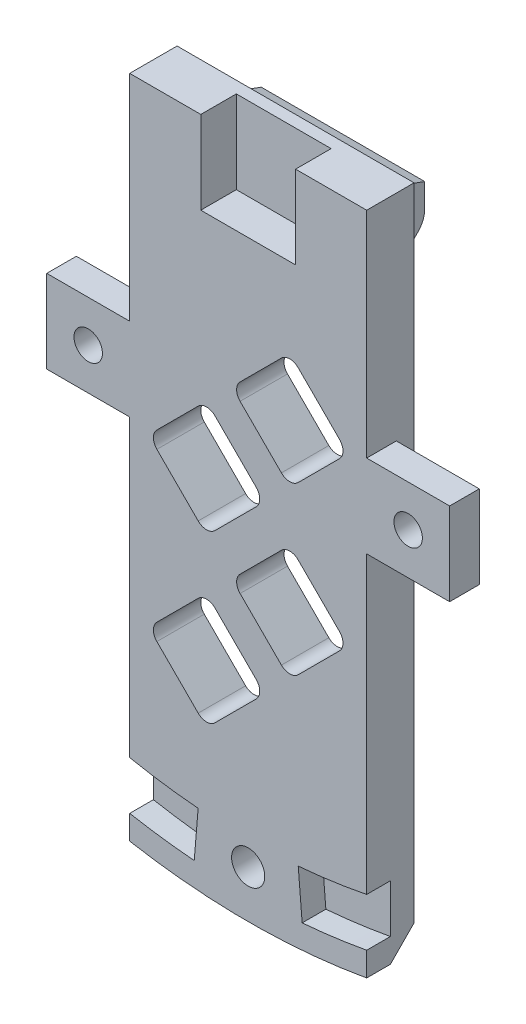
SolidWorks part; units mm, degrees
ref_plane "Front Plane" through (0, 0, 0) normal (0, 0, 1) x (1, 0, 0)
ref_plane "Top Plane" through (0, 0, 0) normal (0, 1, 0) x (1, 0, 0)
ref_plane "Right Plane" through (0, 0, 0) normal (1, 0, 0) x (0, 0, -1)
sketch "Sketch1" plane through (0, 0, 0) normal (0, 0, 1) x (1, 0, 0)
  line L0 (-12.7, -71.2673) -> (-12.7, 71.2673)
  line L1 (12.7, 71.2673) -> (12.7, -71.2673)
  line L2 (-12.7, 0) -> (12.7, 0)
  line L3 (0, 0) -> (0, 40.2261) construction
  arc A0 (-12.7, -71.2673) -> (12.7, -71.2673) centre (0, 0) ccw
  arc A1 (12.7, 71.2673) -> (-12.7, 71.2673) centre (0, 0) ccw
  circle A2 centre (0, 11.43) radius 7.62 construction
  dimension "D1" = 144.78
  dimension "D4" = 15.24
  dimension "D2" = 25.4
  dimension "D3" = 11.43
extrude "Boss-Extrude1" add sketch "Sketch1" along normal blind 5.08 contours L0 A0 L1 L2
sketch "Sketch4" plane through (0, 0, 0) normal (1, 0, 0) x (0, 0, -1)
  line L0 (0, -2.54) -> (5.08, -4.389)
  line L1 (5.08, -4.389) -> (5.08, -6.929)
  line L2 (4.3361, -8.725) -> (0.7439, -12.3171)
  line L3 (0, -14.1132) -> (0, -2.54)
  line L4 (0, -71.2673) -> (0, 0)
  line L5 (0, 0) -> (-5.08, 0)
  line L6 (-5.08, 0) -> (-5.08, -71.2673)
  line L7 (-5.08, -71.2673) -> (0, -71.2673)
  line L8 (0, -71.2673) -> (0, -14.1132)
  line L9 (0, 0) -> (-5.08, 0)
  line L10 (-5.08, 0) -> (-5.08, -71.2673)
  line L11 (-5.08, -71.2673) -> (0, -71.2673)
  arc A0 (0, -14.1132) -> (0.7439, -12.3171) centre (2.54, -14.1132) cw
  arc A1 (4.3361, -8.725) -> (5.08, -6.929) centre (2.54, -6.929) ccw
  dimension "D4" = 2.54
  dimension "D2" = 70
  dimension "D3" = 45
  dimension "D5" = 2.54
  dimension "D6" = 2.54
  dimension "D7" = 5.08
  dimension "D1" = 0
extrude "Boss-Extrude2" add sketch "Sketch4" along normal mid plane 17.526 contours L2 A1 L1 L0 L3 A0
chamfer "Chamfer1" distance 2.54 angle 45 1 edges at (0, -72.39, 0)
sketch "Sketch5" plane through (0, 0, 0) normal (0, 0, -1) x (-1, 0, 0)
  line L0 (-9.788, -42.3613) -> (-5.3581, -46.7913)
  line L1 (-9.788, -40.5653) -> (-5.3581, -36.1353)
  line L2 (-3.562, -46.7913) -> (0.8679, -42.3613)
  line L3 (-3.562, -36.1353) -> (0.8679, -40.5653)
  line L4 (-0.8679, -33.4412) -> (3.562, -37.8712)
  line L5 (-0.8679, -31.6452) -> (3.562, -27.2152)
  line L6 (5.3581, -37.8712) -> (9.788, -33.4412)
  line L7 (5.3581, -27.2152) -> (9.788, -31.6452)
  line L8 (-9.788, -24.5212) -> (-5.3581, -28.9511)
  line L9 (-9.788, -22.7251) -> (-5.3581, -18.2951)
  line L10 (-3.562, -28.9511) -> (0.8679, -24.5212)
  line L11 (-3.562, -18.2951) -> (0.8679, -22.7251)
  line L12 (-0.8679, -51.2814) -> (3.562, -55.7114)
  line L13 (-0.8679, -49.4854) -> (3.562, -45.0554)
  line L14 (5.3581, -55.7114) -> (9.788, -51.2814)
  line L15 (5.3581, -45.0554) -> (9.788, -49.4854)
  line L16 (-12.7, 0) -> (-12.7, -68.6858) construction
  line L17 (12.7, -68.6858) -> (12.7, 0) construction
  line L18 (-8.763, -14.1132) -> (8.763, -14.1132) construction
  arc A0 (-3.562, -36.1353) -> (-5.3581, -36.1353) centre (-4.46, -37.0333) ccw
  arc A1 (0.8679, -40.5653) -> (0.8679, -42.3613) centre (-0.0301, -41.4633) cw
  arc A2 (-3.562, -46.7913) -> (-5.3581, -46.7913) centre (-4.46, -45.8933) cw
  arc A3 (-9.788, -40.5653) -> (-9.788, -42.3613) centre (-8.89, -41.4633) ccw
  arc A4 (9.788, -51.2814) -> (9.788, -49.4854) centre (8.89, -50.3834) ccw
  arc A5 (5.3581, -55.7114) -> (3.562, -55.7114) centre (4.46, -54.8133) cw
  arc A6 (-0.8679, -51.2814) -> (-0.8679, -49.4854) centre (0.0301, -50.3834) cw
  arc A7 (5.3581, -45.0554) -> (3.562, -45.0554) centre (4.46, -45.9534) ccw
  arc A8 (-3.562, -18.2951) -> (-5.3581, -18.2951) centre (-4.46, -19.1932) ccw
  arc A9 (-9.788, -24.5212) -> (-9.788, -22.7251) centre (-8.89, -23.6231) cw
  arc A10 (0.8679, -22.7251) -> (0.8679, -24.5212) centre (-0.0301, -23.6231) cw
  arc A11 (-3.562, -28.9511) -> (-5.3581, -28.9511) centre (-4.46, -28.0531) cw
  arc A12 (5.3581, -37.8712) -> (3.562, -37.8712) centre (4.46, -36.9732) cw
  arc A13 (9.788, -31.6452) -> (9.788, -33.4412) centre (8.89, -32.5432) cw
  arc A14 (5.3581, -27.2152) -> (3.562, -27.2152) centre (4.46, -28.1133) ccw
  arc A15 (-0.8679, -33.4412) -> (-0.8679, -31.6452) centre (0.0301, -32.5432) cw
  point P10 (-4.46, -47.6893)
  point P13 (-10.6861, -41.4633)
  dimension "D2" = 1.27
  dimension "D3" = 1.27
  dimension "D4" = 3.81
  dimension "D5" = 3.81
  dimension "D6" = 3.81
  dimension "D7" = 45
  dimension "D1" = 3.81
  dimension "D8" = 3.81
  dimension "D9" = 5.08
extrude "Cut-Extrude2" cut sketch "Sketch5" against normal blind 6.35
sketch "Sketch6" plane through (0, 0, 5.08) normal (0, 0, 1) x (1, 0, 0)
  line L0 (-12.7, 0) -> (12.7, 0) construction
  line L1 (-5.08, 0) -> (5.08, 0)
  line L2 (-5.08, 0) -> (-5.08, -8.89)
  line L3 (-5.08, -8.89) -> (5.08, -8.89)
  line L4 (5.08, 0) -> (5.08, -8.89)
  line L5 (-5.08, 0) -> (5.08, -8.89) construction
  line L6 (-5.08, -8.89) -> (5.08, 0) construction
  line L7 (-12.7, -71.2673) -> (-12.7, 0) construction
  line L8 (12.7, 0) -> (12.7, -71.2673) construction
  point P4 (0, -4.445)
  dimension "D1" = 8.89
  dimension "D2" = 7.62
  dimension "D3" = 7.62
extrude "Cut-Extrude3" cut sketch "Sketch6" against normal blind 3.81
sketch "Sketch7" plane through (0, 0, 0) normal (0, 0, -1) x (-1, 0, 0)
  line L0 (-18.0352, -72.39) -> (15.5567, -72.39) construction
  line L1 (-12.7, -58.4621) -> (12.7, -58.4621) construction
  line L2 (-12.7, 0) -> (-12.7, -68.6858) construction
  line L3 (12.7, -68.6858) -> (12.7, 0) construction
  circle A0 centre (0, -67.31) radius 4.953
  arc A1 (-12.7, -71.2673) -> (12.7, -71.2673) centre (0, 0) ccw construction
  dimension "D1" = 9.906
  dimension "D2" = 5.08
  dimension "D3" = 25.4
  dimension "D4" = 12.7
extrude "Cut-Extrude4" cut sketch "Sketch7" against normal blind 2.54
sketch "Sketch8" plane through (0, 0, 2.54) normal (0, 0, -1) x (-1, 0, 0)
  circle A0 centre (0, 0) radius 1.7867
  circle A2 centre (0, -67.31) radius 1.778
  dimension "D1" = 3.556
extrude "Cut-Extrude5" cut sketch "Sketch8" against normal through all
sketch "Sketch9" plane through (0, 0, 5.08) normal (0, 0, 1) x (1, 0, 0)
  line L0 (-12.7, -71.2673) -> (-12.7, 0) construction
  line L1 (12.7, 0) -> (12.7, -71.2673) construction
  line L2 (0, 0) -> (5.7842, -69.6101) construction
  line L3 (0, -69.85) -> (0, 0) construction
  line L4 (0, 0) -> (-5.7842, -69.6101) construction
  line L5 (-12.7, -68.6858) -> (-12.7, -63.5127)
  line L6 (-5.7842, -69.6101) -> (-5.3635, -64.5475)
  line L7 (5.7842, -69.6101) -> (5.3635, -64.5475)
  line L8 (12.7, -68.6858) -> (12.7, -63.5127)
  arc A0 (-12.7, -68.6858) -> (-5.7842, -69.6101) centre (0, 0) ccw
  arc A1 (-12.7, -63.5127) -> (-5.3635, -64.5475) centre (0, 0) ccw
  arc A2 (5.7842, -69.6101) -> (12.7, -68.6858) centre (0, 0) ccw
  arc A3 (5.3635, -64.5475) -> (12.7, -63.5127) centre (0, 0) ccw
  dimension "D1" = 64.77
  dimension "D2" = 69.85
  dimension "D3" = 9.5
  dimension "D4" = 4.75
extrude "Cut-Extrude6" cut sketch "Sketch9" against normal blind 2.54
sketch "Sketch10" plane through (0, 0, 0) normal (0, 0, -1) x (-1, 0, 0)
  line L0 (-3.562, -53.9755) -> (0.8679, -58.4054)
  line L1 (-5.3581, -53.9755) -> (-9.788, -58.4054)
  line L2 (0.8679, -60.2015) -> (-3.562, -64.6315)
  line L3 (-9.788, -60.2015) -> (-5.3581, -64.6315)
  line L4 (8.0521, -40.5653) -> (12.4821, -36.1353)
  line L5 (8.0521, -42.3613) -> (12.4821, -46.7913)
  line L6 (14.2782, -36.1353) -> (18.7081, -40.5653)
  line L7 (14.2782, -46.7913) -> (18.7081, -42.3613)
  line L8 (12.4821, -28.9511) -> (8.0521, -24.5212)
  line L9 (14.2782, -28.9511) -> (18.7081, -24.5212)
  line L10 (8.0521, -22.7251) -> (12.4821, -18.2951)
  line L11 (18.7081, -22.7251) -> (14.2782, -18.2951)
  line L12 (3.562, -20.031) -> (-0.8679, -15.6011)
  line L13 (5.3581, -20.031) -> (9.788, -15.6011)
  line L14 (-0.8679, -13.805) -> (3.562, -9.3751)
  line L15 (9.788, -13.805) -> (5.3581, -9.3751)
  line L16 (-8.0521, -33.4412) -> (-12.4821, -37.8712)
  line L17 (-8.0521, -31.6452) -> (-12.4821, -27.2152)
  line L18 (-14.2782, -37.8712) -> (-18.7081, -33.4412)
  line L19 (-14.2782, -27.2152) -> (-18.7081, -31.6452)
  line L20 (9.788, -49.4854) -> (5.3581, -45.0554) construction
  line L21 (5.3581, -55.7114) -> (9.788, -51.2814) construction
  line L22 (-0.8679, -51.2814) -> (3.562, -55.7114) construction
  line L23 (3.562, -45.0554) -> (-0.8679, -49.4854) construction
  line L24 (9.788, -49.4854) -> (5.3581, -45.0554)
  line L25 (5.3581, -55.7114) -> (9.788, -51.2814)
  line L26 (-0.8679, -51.2814) -> (3.562, -55.7114)
  line L27 (3.562, -45.0554) -> (-0.8679, -49.4854)
  line L28 (-5.3581, -36.1353) -> (-9.788, -40.5653) construction
  line L29 (9.788, -31.6452) -> (5.3581, -27.2152) construction
  line L30 (0.8679, -22.7251) -> (-3.562, -18.2951) construction
  line L31 (-0.8679, -33.4412) -> (3.562, -37.8712) construction
  line L32 (-3.562, -28.9511) -> (0.8679, -24.5212) construction
  line L33 (3.562, -27.2152) -> (-0.8679, -31.6452) construction
  line L34 (5.3581, -37.8712) -> (9.788, -33.4412) construction
  line L35 (0.8679, -40.5653) -> (-3.562, -36.1353) construction
  line L36 (-3.562, -46.7913) -> (0.8679, -42.3613) construction
  line L37 (-5.3581, -18.2951) -> (-9.788, -22.7251) construction
  line L38 (-9.788, -42.3613) -> (-5.3581, -46.7913) construction
  line L39 (12.7, -68.6858) -> (12.7, 0) construction
  line L40 (-10.795, -16.0182) -> (10.795, -16.0182)
  line L41 (-10.795, -16.0182) -> (-10.795, -62.357)
  line L42 (-10.795, -62.357) -> (10.795, -62.357)
  line L43 (10.795, -16.0182) -> (10.795, -62.357)
  line L44 (-10.795, -16.0182) -> (10.795, -62.357) construction
  line L45 (-10.795, -62.357) -> (10.795, -16.0182) construction
  line L46 (-12.7, 0) -> (-12.7, -68.6858) construction
  line L47 (-8.763, -14.1132) -> (8.763, -14.1132) construction
  line L48 (-18.7081, -51.2814) -> (-14.2782, -55.7114)
  line L49 (-18.7081, -49.4854) -> (-14.2782, -45.0554)
  line L50 (-12.4821, -55.7114) -> (-8.0521, -51.2814)
  line L51 (-12.4821, -45.0554) -> (-8.0521, -49.4854)
  line L52 (18.7081, -60.2015) -> (14.2782, -64.6315)
  line L53 (18.7081, -58.4054) -> (14.2782, -53.9755)
  line L54 (12.4821, -64.6315) -> (8.0521, -60.2015)
  line L55 (12.4821, -53.9755) -> (8.0521, -58.4054)
  arc A0 (5.3581, -45.0554) -> (3.562, -45.0554) centre (4.46, -45.9534) ccw construction
  arc A1 (9.788, -51.2814) -> (9.788, -49.4854) centre (8.89, -50.3834) ccw construction
  arc A2 (3.562, -55.7114) -> (5.3581, -55.7114) centre (4.46, -54.8133) ccw construction
  arc A3 (-0.8679, -49.4854) -> (-0.8679, -51.2814) centre (0.0301, -50.3834) ccw construction
  arc A4 (5.3581, -45.0554) -> (3.562, -45.0554) centre (4.46, -45.9534) ccw
  arc A5 (9.788, -51.2814) -> (9.788, -49.4854) centre (8.89, -50.3834) ccw
  arc A6 (3.562, -55.7114) -> (5.3581, -55.7114) centre (4.46, -54.8133) ccw
  arc A7 (-0.8679, -49.4854) -> (-0.8679, -51.2814) centre (0.0301, -50.3834) ccw
  arc A8 (-18.7081, -31.6452) -> (-18.7081, -33.4412) centre (-17.8101, -32.5432) ccw
  arc A9 (18.7081, -22.7251) -> (18.7081, -24.5212) centre (17.8101, -23.6231) cw
  arc A10 (14.2782, -28.9511) -> (12.4821, -28.9511) centre (13.3801, -28.0531) cw
  arc A11 (12.4821, -18.2951) -> (14.2782, -18.2951) centre (13.3801, -19.1932) cw
  arc A12 (9.788, -15.6011) -> (9.788, -13.805) centre (8.89, -14.703) ccw
  arc A13 (5.3581, -9.3751) -> (3.562, -9.3751) centre (4.46, -10.2731) ccw
  arc A14 (-0.8679, -13.805) -> (-0.8679, -15.6011) centre (0.0301, -14.703) ccw
  arc A15 (-12.4821, -27.2152) -> (-14.2782, -27.2152) centre (-13.3801, -28.1133) ccw
  arc A16 (-14.2782, -37.8712) -> (-12.4821, -37.8712) centre (-13.3801, -36.9732) ccw
  arc A17 (12.4821, -46.7913) -> (14.2782, -46.7913) centre (13.3801, -45.8933) ccw
  arc A18 (18.7081, -42.3613) -> (18.7081, -40.5653) centre (17.8101, -41.4633) ccw
  arc A19 (14.2782, -36.1353) -> (12.4821, -36.1353) centre (13.3801, -37.0333) ccw
  arc A20 (8.0521, -40.5653) -> (8.0521, -42.3613) centre (8.9502, -41.4633) ccw
  arc A21 (-9.788, -58.4054) -> (-9.788, -60.2015) centre (-8.89, -59.3035) ccw
  arc A22 (-5.3581, -64.6315) -> (-3.562, -64.6315) centre (-4.46, -63.7334) ccw
  arc A23 (0.8679, -60.2015) -> (0.8679, -58.4054) centre (-0.0301, -59.3035) ccw
  arc A24 (-5.3581, -53.9755) -> (-3.562, -53.9755) centre (-4.46, -54.8735) cw
  arc A25 (5.3581, -20.031) -> (3.562, -20.031) centre (4.46, -19.133) cw
  arc A26 (8.0521, -22.7251) -> (8.0521, -24.5212) centre (8.9502, -23.6231) ccw
  arc A27 (-8.0521, -31.6452) -> (-8.0521, -33.4412) centre (-8.9502, -32.5432) cw
  arc A28 (4.3295, -69.7157) -> (-4.3295, -69.7157) centre (0, -67.31) ccw construction
  arc A29 (-12.4821, -55.7114) -> (-14.2782, -55.7114) centre (-13.3801, -54.8133) cw
  arc A30 (-8.0521, -51.2814) -> (-8.0521, -49.4854) centre (-8.9502, -50.3834) ccw
  arc A31 (-12.4821, -45.0554) -> (-14.2782, -45.0554) centre (-13.3801, -45.9534) ccw
  arc A32 (-18.7081, -49.4854) -> (-18.7081, -51.2814) centre (-17.8101, -50.3834) ccw
  arc A33 (8.0521, -58.4054) -> (8.0521, -60.2015) centre (8.9502, -59.3035) ccw
  arc A34 (12.4821, -64.6315) -> (14.2782, -64.6315) centre (13.3801, -63.7334) ccw
  arc A35 (18.7081, -60.2015) -> (18.7081, -58.4054) centre (17.8101, -59.3035) ccw
  arc A36 (14.2782, -53.9755) -> (12.4821, -53.9755) centre (13.3801, -54.8735) ccw
  point P98 (0, -39.1876)
  dimension "D3" = 1.27
  dimension "D4" = 3.81
  dimension "D5" = 3.81
  dimension "D6" = 3.81
  dimension "D1" = 1.27
  dimension "D10" = 1.27
  dimension "D11" = 1.27
  dimension "D2" = 6.2649
  dimension "D7" = 1.905
  dimension "D8" = 1.905
  dimension "D9" = 1.905
  dimension "D12" = 3.81
extrude "Cut-Extrude7" cut sketch "Sketch10" against normal blind 0.762 contours L50 A30 L51 L41 | A24 L1 A21 L3 L42 L2 A23 L0 | L4 A20 L5 L43 | A27 L17 L41 L16 | A25 L13 L40 L12 | L10 A26 L8 L43 | L55 A33 L54 L42 L43
sketch "Sketch11" plane through (0, 0, 5.08) normal (0, 0, 1) x (1, 0, 0)
  line L0 (12.7, 0) -> (12.7, -63.5127) construction
  line L1 (12.7, -23.0073) -> (21.59, -23.0073)
  line L2 (12.7, -23.0073) -> (12.7, -31.8973)
  line L3 (12.7, -31.8973) -> (21.59, -31.8973)
  line L4 (21.59, -23.0073) -> (21.59, -31.8973)
  line L5 (12.7, -23.0073) -> (21.59, -31.8973) construction
  line L6 (12.7, -31.8973) -> (21.59, -23.0073) construction
  line L7 (-12.7, -63.5127) -> (-12.7, 0) construction
  line L8 (-12.7, -23.0073) -> (-21.59, -23.0073)
  line L9 (-12.7, -23.0073) -> (-12.7, -31.8973)
  line L10 (-12.7, -31.8973) -> (-21.59, -31.8973)
  line L11 (-21.59, -23.0073) -> (-21.59, -31.8973)
  line L12 (-12.7, -23.0073) -> (-21.59, -31.8973) construction
  line L13 (-12.7, -31.8973) -> (-21.59, -23.0073) construction
  circle A0 centre (-17.145, -27.4523) radius 1.524
  circle A1 centre (17.145, -27.4523) radius 1.524
  point P4 (17.145, -27.4523)
  point P11 (-17.145, -27.4523)
  dimension "D3" = 3.048
  dimension "D1" = 48.26
  dimension "D2" = 8.89
extrude "Boss-Extrude3" add sketch "Sketch11" against normal blind 3.175
equation "\"D5@Sketch5\"=\"D4@Sketch5\""
equation "\"D4@Sketch5\"=\"D6@Sketch5\""
equation "\"D8@Sketch5\"=\"D1@Sketch5\""
equation "\"D2@Sketch6\"=\"D3@Sketch6\""
equation "\"D4@Sketch7\"=\"D3@Sketch7\"/2"
equation "\"D4@Sketch9\"=\"D3@Sketch9\"/2"
equation "\"D5@Sketch10\"=\"D4@Sketch10\""
equation "\"D6@Sketch10\"=\"D4@Sketch10\""
equation "\"D8@Sketch10\"=\"D7@Sketch10\""
equation "\"D9@Sketch10\"=\"D7@Sketch10\""
equation "\"D12@Sketch10\"=\"D4@Sketch10\""
